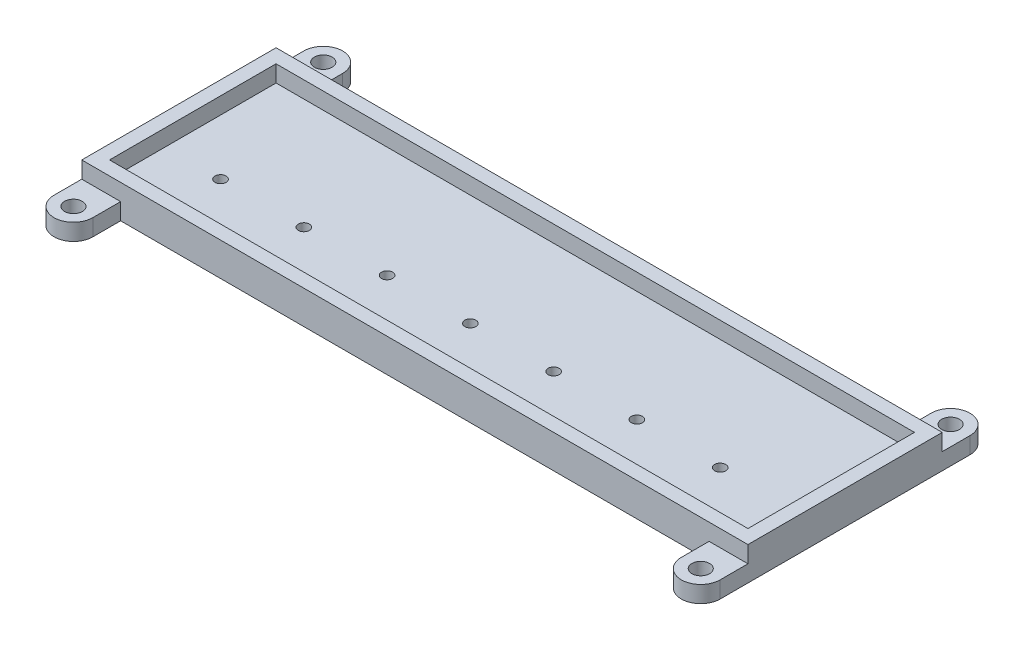
SolidWorks part; units mm, degrees
ref_plane "Front Plane" through (0, 0, 0) normal (0, 0, 1) x (1, 0, 0)
ref_plane "Top Plane" through (0, 0, 0) normal (0, 1, 0) x (1, 0, 0)
ref_plane "Right Plane" through (0, 0, 0) normal (1, 0, 0) x (0, 0, -1)
sketch "Sketch1" plane through (0, 0, 0) normal (0, 1, 0) x (1, 0, 0)
  line L1 (0, 0) -> (115, 0)
  line L2 (0, 0) -> (0, 30)
  line L3 (0, 30) -> (115, 30)
  line L4 (115, 0) -> (115, 30)
  line L5 (0, 0) -> (115, 30) construction
  line L6 (0, 30) -> (115, 0) construction
  point P4 (57.5, 15)
  dimension "D1" = 30
  dimension "D2" = 115
extrude "Boss-Extrude1" add sketch "Sketch1" along normal blind 3
sketch "Sketch2" plane through (0, 0, 0) normal (0, 1, 0) x (1, 0, 0)
  line L8 (-2.5, 32.5) -> (-2.5, -2.5)
  line L9 (-2.5, -2.5) -> (117.5, -2.5)
  line L10 (117.5, -2.5) -> (117.5, 32.5)
  line L11 (117.5, 32.5) -> (-2.5, 32.5)
  line L12 (-2.5, 32.5) -> (-2.5, -2.5)
  line L13 (-2.5, -2.5) -> (117.5, -2.5)
  line L14 (117.5, -2.5) -> (117.5, 32.5)
  line L15 (117.5, 32.5) -> (-2.5, 32.5)
  line L16 (0, 30) -> (0, 0)
  line L17 (0, 0) -> (115, 0)
  line L18 (115, 0) -> (115, 30)
  line L19 (115, 30) -> (0, 30)
  line L20 (0, 30) -> (0, 0)
  line L21 (0, 0) -> (115, 0)
  line L22 (115, 0) -> (115, 30)
  line L23 (115, 30) -> (0, 30)
  dimension "D1" = 2.5
  dimension "D2" = 0
extrude "Boss-Extrude3" add sketch "Sketch2" along normal offset from surface (6 mm away) 3 up to face at (57.5, 3, -15) offset beyond the face yes
ref_plane "Plane1" through (0, 0, -10) normal (0, 0, 1) x (1, 0, 0)
ref_plane "Plane2" through (0, 0, -20) normal (0, 0, 1) x (1, 0, 0)
sketch "Sketch4" plane through (0, 3, 0) normal (0, 1, 0) x (1, 0, 0)
  circle A1 centre (10, 10) radius 1
  dimension "D1" = 2
  dimension "D2" = 10
  dimension "D3" = 10
extrude "Cut-Extrude1" cut sketch "Sketch4" against normal through all and the other way through all contours A1
pattern_linear "LPattern1" count 7 spacing 15 along (1, 0, 0) of "Cut-Extrude1"
sketch "Sketch5" plane through (0, 0, 0) normal (0, 1, 0) x (1, 0, 0)
  line L0 (-2.5, -2.5) -> (-2.5, -7.5)
  line L1 (4.5, -2.5) -> (-2.5, -2.5)
  line L2 (117.5, -2.5) -> (-2.5, -2.5) construction
  line L3 (4.5, -2.5) -> (4.5, -7.5)
  arc A0 (-2.5, -7.5) -> (4.5, -7.5) centre (1, -7.5) ccw
  circle A1 centre (1, -7.5) radius 1.6
  dimension "D2" = 7
  dimension "D3" = 3.2
  dimension "D1" = 5
extrude "Boss-Extrude4" add sketch "Sketch5" along normal blind 3
ref_plane "Plane3" through (0, 0, -15) normal (0, 0, 1) x (1, 0, 0)
ref_plane "Plane4" through (57.5, 0, 0) normal (-1, 0, 0) x (0, 0, 1)
mirror "Mirror1" about plane through (0, 0, -15) normal (0, 0, 1) of "Boss-Extrude4"
mirror "Mirror2" about plane through (57.5, 0, 0) normal (-1, 0, 0) of "Mirror1", "Boss-Extrude4"
